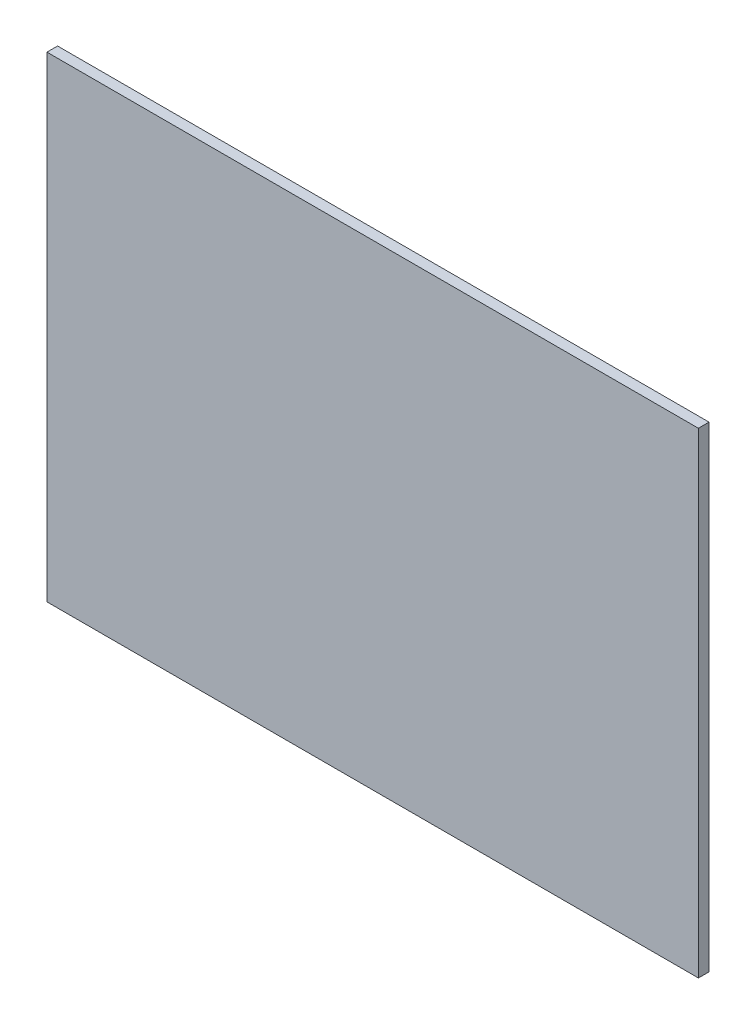
SolidWorks part; units mm, degrees
ref_plane "Front Plane" through (0, 0, 0) normal (0, 0, 1) x (1, 0, 0)
ref_plane "Top Plane" through (0, 0, 0) normal (0, 1, 0) x (1, 0, 0)
ref_plane "Right Plane" through (0, 0, 0) normal (1, 0, 0) x (0, 0, -1)
sketch "Sketch1" plane through (0, 0, 0) normal (0, 0, 1) x (1, 0, 0)
  line L1 (61.3, -44.8) -> (-61.3, -44.8)
  line L2 (61.3, -44.8) -> (61.3, 44.8)
  line L3 (61.3, 44.8) -> (-61.3, 44.8)
  line L4 (-61.3, -44.8) -> (-61.3, 44.8)
  line L5 (61.3, -44.8) -> (-61.3, 44.8) construction
  line L6 (61.3, 44.8) -> (-61.3, -44.8) construction
  point P0 (0, 0)
  dimension "D1" = 89.6
  dimension "D2" = 122.6
extrude "Boss-Extrude1" add sketch "Sketch1" along normal blind 2
